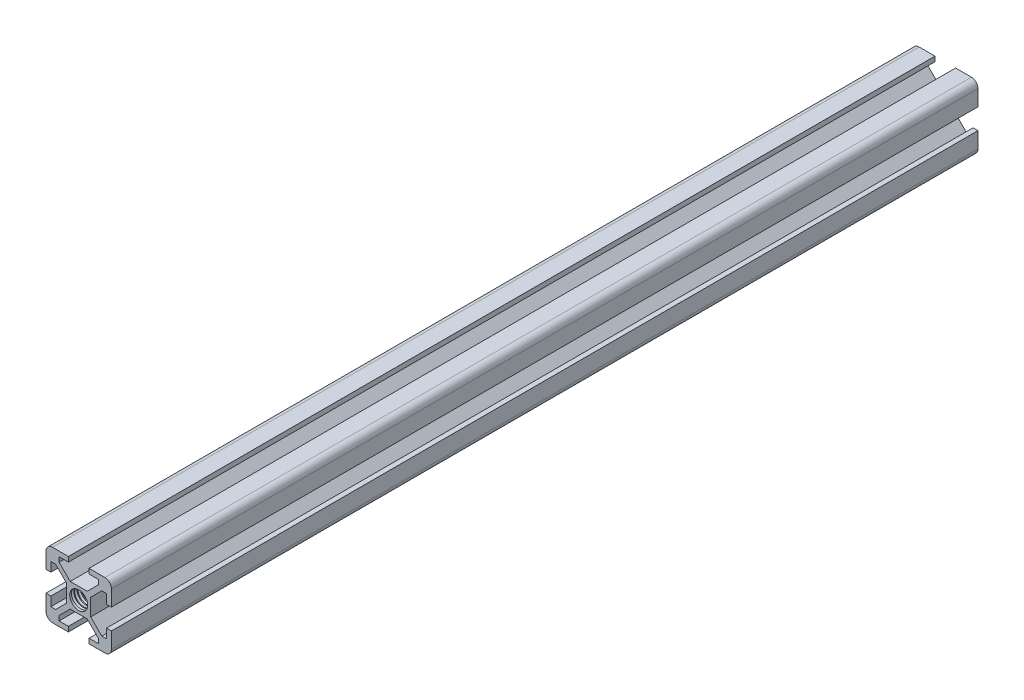
SolidWorks part; units mm, degrees
material "1060 Alloy"
ref_plane "Front Plane" through (0, 0, 0) normal (0, 0, 1) x (1, 0, 0)
ref_plane "Top Plane" through (0, 0, 0) normal (0, 1, 0) x (1, 0, 0)
ref_plane "Right Plane" through (0, 0, 0) normal (1, 0, 0) x (0, 0, -1)
sketch "Sketch1" plane through (0, 0, 0) normal (0, 0, 1) x (1, 0, 0)
  line L0 (0, 0) -> (3.66, 3.66) construction
  line L1 (-2.5993, -3.66) -> (2.5993, -3.66)
  line L2 (-3.66, -2.5993) -> (-3.66, 2.5993)
  line L3 (-2.5993, 3.66) -> (2.5993, 3.66)
  line L4 (3.66, -2.5993) -> (3.66, 2.5993)
  line L5 (-3.66, -3.66) -> (3.66, 3.66) construction
  line L6 (-3.66, 3.66) -> (3.66, -3.66) construction
  line L7 (-8, -10) -> (-3.15, -10)
  line L8 (-10, -8) -> (-10, -3.15)
  line L9 (-8, 10) -> (-3.15, 10)
  line L10 (10, -8) -> (10, -3.15)
  line L11 (-10, -10) -> (3.66, 3.66) construction
  line L12 (-10, 10) -> (9.4142, -9.4142) construction
  line L13 (0.5303, -0.5303) -> (1.0607, 0) construction
  line L14 (-0.5303, 0.5303) -> (0, 1.0607) construction
  line L15 (-0.5303, 0.5303) -> (9.4697, 10.5303) construction
  line L16 (0.5303, -0.5303) -> (10.5303, 9.4697) construction
  line L17 (0, 0) -> (10, 0) construction
  line L18 (-10, -3.15) -> (-8.5, -3.15)
  line L19 (8.5, 3.15) -> (8.5, 5.995)
  line L20 (10, 3.15) -> (10, 8)
  line L21 (8.5, 5.995) -> (7.0557, 5.995)
  line L22 (9.4142, 9.4142) -> (10, 10) construction
  line L23 (0, 0) -> (10, 10) construction
  line L24 (9.4142, 9.4142) -> (10, 10) construction
  line L25 (0, 14.5751) -> (0, -10) construction
  line L26 (0, 0) -> (11.8172, 11.8172) construction
  line L27 (3.15, 10) -> (8, 10)
  line L28 (5.995, 8.5) -> (5.995, 7.0557)
  line L29 (10, 3.15) -> (8.5, 3.15)
  line L30 (3.15, 8.5) -> (5.995, 8.5)
  line L31 (9.8413, 8.7807) -> (10, 8.9393)
  line L32 (8.7807, 9.8413) -> (8.9393, 10)
  line L33 (0.5303, 0.5303) -> (1.0607, 0) construction
  line L34 (-0.5303, -0.5303) -> (0, -1.0607) construction
  line L35 (5.995, -8.5) -> (5.995, -7.0557)
  line L36 (3.15, -8.5) -> (5.995, -8.5)
  line L38 (-8, -10) -> (-3.15, -10)
  line L39 (8.5, -5.995) -> (7.0557, -5.995)
  line L40 (8.5, -3.15) -> (8.5, -5.995)
  line L42 (10, -3.15) -> (10, -8)
  line L43 (-8.5, -5.995) -> (-7.0557, -5.995)
  line L44 (-8.5, -3.15) -> (-8.5, -5.995)
  line L45 (-10, 3.15) -> (-8.5, 3.15)
  line L46 (-10, -8) -> (-10, -3.15)
  line L47 (8, -10) -> (3.15, -10)
  line L48 (10, -3.15) -> (8.5, -3.15)
  line L49 (-3.15, -8.5) -> (-5.995, -8.5)
  line L50 (-0.5303, 0.5303) -> (-1.0607, 0) construction
  line L51 (0.5303, -0.5303) -> (0, -1.0607) construction
  line L52 (-5.995, -8.5) -> (-5.995, -7.0557)
  line L53 (-10, 3.15) -> (-10, 8)
  line L54 (3.15, -10) -> (3.15, -8.5)
  line L55 (-8.5, 5.995) -> (-7.0557, 5.995)
  line L56 (-8.5, 3.15) -> (-8.5, 5.995)
  line L57 (-0.5303, -0.5303) -> (-1.0607, 0) construction
  line L58 (0.5303, 0.5303) -> (0, 1.0607) construction
  line L59 (-5.995, 8.5) -> (-5.995, 7.0557)
  line L60 (-3.15, 8.5) -> (-5.995, 8.5)
  line L61 (-3.15, -10) -> (-3.15, -8.5)
  line L62 (8, 10) -> (3.15, 10)
  line L63 (-10, 3.15) -> (-10, 8)
  line L64 (3.15, -10) -> (8, -10)
  line L65 (3.15, -10) -> (8, -10)
  line L66 (-3.15, -10) -> (-8, -10)
  line L67 (-2.5993, 3.66) -> (-5.995, 7.0557)
  line L68 (-3.66, 2.5993) -> (-7.0557, 5.995)
  line L69 (-3.66, -2.5993) -> (-7.0557, -5.995)
  line L70 (-2.5993, -3.66) -> (-5.995, -7.0557)
  line L71 (2.5993, -3.66) -> (5.995, -7.0557)
  line L72 (3.66, -2.5993) -> (7.0557, -5.995)
  line L73 (3.66, 2.5993) -> (7.0557, 5.995)
  line L74 (2.5993, 3.66) -> (5.995, 7.0557)
  line L75 (3.15, 10) -> (8, 10)
  line L76 (-3.15, 10) -> (-8, 10)
  line L78 (3.15, 10) -> (3.15, 8.5)
  line L79 (-3.15, 10) -> (-3.15, 8.5)
  circle A0 centre (0, 0) radius 2.75
  arc A1 (8, 10) -> (10, 8) centre (8, 8) cw
  arc A2 (8, -10) -> (10, -8) centre (8, -8) ccw
  arc A3 (-8, -10) -> (-10, -8) centre (-8, -8) cw
  arc A4 (-8, 10) -> (-10, 8) centre (-8, 8) ccw
  dimension "D1" = 5.5
  dimension "D6" = 2
  dimension "D2" = 7.32
  dimension "D3" = 20
  dimension "D7" = 2.845
  dimension "D9" = 20
  dimension "D12" = 1.4443
  dimension "D13" = 7.32
  dimension "D14" = 3.66
  dimension "D4" = 3.15
  dimension "D5" = 1.5
  dimension "D15" = 4.85
  dimension "D16" = 5.1987
  dimension "D17" = 3.66
  dimension "D18" = 2.845
  dimension "D19" = 6.3
extrude "Boss-Extrude1" add sketch "Sketch1" along normal blind 265 contours L9 A4 L53 L45 L56 L55 L68 L2 L69 L43 L44 L18 L8 A3 L7 L61 L49 L52 L70 L1 L71 L35 L36 L54 L47 A2 L10 L48 L40 L39 L72 L4 L73 L21 L19 L29 L20 A1 L27 L78 L30 L28 L74 L3 L67 L59 L60 L79
ref_plane "Plane1" through (0, 0, 1) normal (0, 0, -1) x (-1, 0, 0)
sketch "Sketch2" plane through (0, 0, 1) normal (0, 0, -1) x (-1, 0, 0)
  circle A0 centre (0, 0) radius 2.15
curve "Helix/Spiral1" pitch 1 height 18.5 turns 18.5
sketch "Sketch3" plane through (0, 0, 0) normal (1, 0, 0) x (0, 0, -1)
  line L0 (-2.2297, 2.75) -> (-0.65, 2.75) construction
  line L1 (0, 2.75) -> (-265, 2.75) construction
  line L2 (-0.65, 3.3895) -> (-1.025, 2.74)
  line L3 (-1.025, 2.74) -> (-0.275, 2.74)
  line L4 (-0.275, 2.74) -> (-0.65, 3.3895)
  line L5 (0, -2.5993) -> (0, 2.5993) construction
  circle A0 centre (-0.65, 2.9565) radius 0.2165 construction
  dimension "D1" = 0.75
  dimension "D2" = 0.65
  dimension "D3" = 0.01
  dimension "D4" = 0
sweep "Cut-Sweep2" cut profiles "Sketch3" path "Helix/Spiral1"
ref_plane "Plane2" through (0, 0, 132.5) normal (0, 0, -1) x (-1, 0, 0)
mirror "Mirror1" about plane through (0, 0, 132.5) normal (0, 0, -1) of "Cut-Sweep2"
